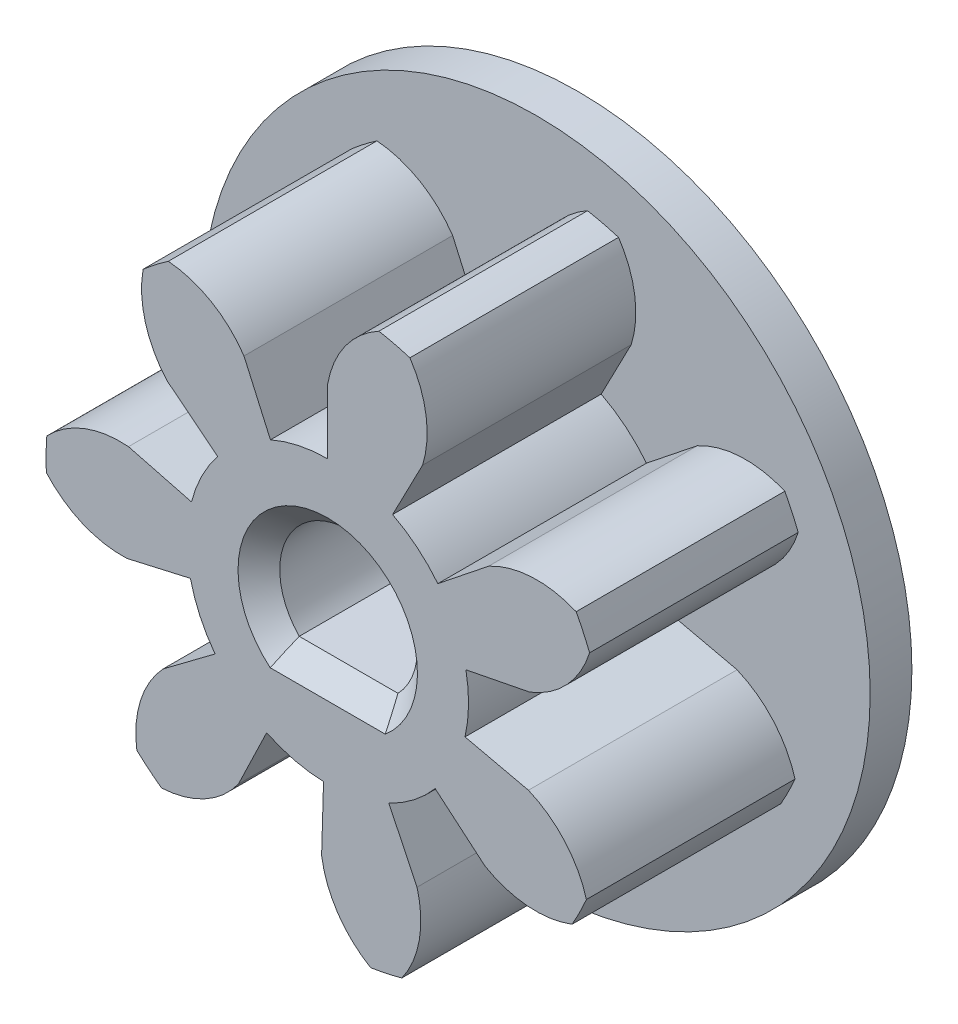
SolidWorks part; units mm, degrees
ref_plane "Front Plane" through (0, 0, 0) normal (0, 0, 1) x (1, 0, 0)
ref_plane "Top Plane" through (0, 0, 0) normal (0, 1, 0) x (1, 0, 0)
ref_plane "Right Plane" through (0, 0, 0) normal (1, 0, 0) x (0, 0, -1)
sketch "Sketch2" plane through (0, 0, 0) normal (0, 0, 1) x (1, 0, 0)
  circle A0 centre (0, 0) radius 6.75
  dimension "D1" = 13.5
extrude "gear outside diameter" add sketch "Sketch2" along normal blind 5
sketch "Sketch1" plane through (0, 0, 0) normal (0, 0, 1) x (1, 0, 0)
  line L0 (0, 4.9334) -> (0, 0) construction
  line L1 (0, 0) -> (0.0782, 5.2494) construction
  line L2 (0, 0) -> (1.226, 6.6377) construction
  line L3 (0, 0) -> (-3.2411, 15.2439) construction
  line L4 (0, 4.9334) -> (0, 3.375)
  line L5 (-2.0071, 4.5066) -> (-1.3731, 3.0831)
  circle A0 centre (0, 0) radius 6.75 construction
  circle A1 centre (0, 0) radius 5.25 construction
  circle A2 centre (0, 0) radius 4.9334 construction
  arc A3 (1.226, 6.6377) -> (0, 4.9334) centre (2.3857, 4.5104) ccw
  arc A4 (-3.8204, 5.5648) -> (-2.0071, 4.5066) centre (-4.0143, 3.1497) cw
  arc A5 (-3.8204, 5.5648) -> (1.226, 6.6377) centre (0, 0) cw
  arc A6 (0, 3.375) -> (-1.3731, 3.0831) centre (0, 0) ccw
  dimension "D1" = 13.5
  dimension "D2" = 10.5
  dimension "D3" = 9.8668
  dimension "D7" = 6.75
  dimension "D4" = 12.857
  dimension "D5" = 0.854
  dimension "D6" = 10.464
extrude "gear tooth cut" cut sketch "Sketch1" along normal through all
pattern_circular "gear teeth" count 7 over 360 about axis through (0, 0, 0) along (0, 0, 1) of "gear tooth cut"
sketch "Sketch3" plane through (0, 0, 0) normal (0, 0, 1) x (1, 0, 0)
  circle A0 centre (0, 0) radius 3.375
  dimension "D1" = 6.75
extrude "gear dedendum circle" add sketch "Sketch3" along normal up to surface (5 mm away) up to face at (0, 0, 5)
sketch "Sketch5" plane through (0, 0, 0) normal (0, 0, -1) x (-1, 0, 0)
  circle A0 centre (0, 0) radius 8
  dimension "D1" = 16
extrude "Boss-Extrude1" add sketch "Sketch5" along normal blind 1
sketch "Sketch4" plane through (0, 0, 5) normal (0, 0, 1) x (1, 0, 0)
  line L0 (-1.1832, -1.15) -> (1.1832, -1.15)
  arc A0 (1.1832, -1.15) -> (-1.1832, -1.15) centre (0, 0) ccw
  point P5 (0, 1.65)
  dimension "D1" = 3.3
  dimension "D2" = 2.8
extrude "Cut-Extrude1" cut sketch "Sketch4" against normal through all
chamfer "Chamfer1" [suppressed] distance 1.5 angle 45
chamfer "Chamfer2" distance 0.5 angle 45 4 edges at (0, -1.15, 5) (0, 1.65, 5) (0, -1.15, -1) (0, 1.65, -1)
equation "\"N\"= 7'Number of teeth"
equation "\"m\"= 1.5'module  (using 25.4/P for imperial gears)"
equation "\"F\"= 5'face width"
equation "\"phi\"=20 'pressure angle"
equation "\"d\"=\"N\"*\"m\""
equation "\"OD\"=(\"N\"+2)*\"m\""
equation "\"db\"=\"d\"* cos( \"phi\" ) "
equation "\"D5@Sketch1\"= (tan( \"phi\" )-\"phi\" * pi /180)*180/ pi "
equation "\"D2@Sketch1\" = \"d\""
equation "\"D3@Sketch1\"=\"db\""
equation "\"D1@Sketch1\"=\"OD\""
equation "\"phiB\"= arccos( \"db\"/\"OD\" ) "
equation "\"D6@Sketch1\"=tan(\"phiB\")*180 /  pi -\"phiB\""
equation "\"D4@Sketch1\" = 360/\"N\"/4"
equation "\"D1@Sketch2\" = \"OD\""
equation "\"D1@gear teeth\"=\"N\""
equation "\"x\"=2.5-\"N\"*(1-cos(\"phi\"))"
equation "\"D1@Sketch3\" = (\"N\"-2.5)*\"m\""
equation "\"D7@Sketch1\" = (\"N\"-2.5)*\"m\""
equation "\"D1@gear outside diameter\" = \"F\""
